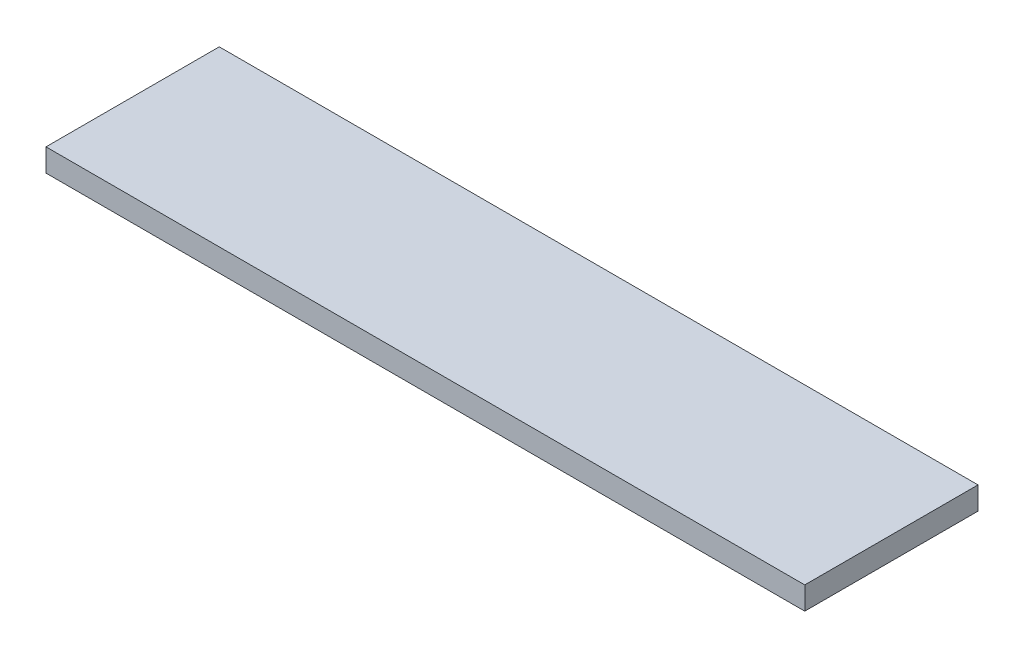
SolidWorks part; units mm, degrees
ref_plane "Спереди" through (0, 0, 0) normal (0, 0, 1) x (1, 0, 0)
ref_plane "Сверху" through (0, 0, 0) normal (0, 1, 0) x (1, 0, 0)
ref_plane "Справа" through (0, 0, 0) normal (1, 0, 0) x (0, 0, -1)
sketch "Эскиз1" plane through (0, 0, 0) normal (0, 1, 0) x (1, 0, 0)
  line L1 (300, -68.5) -> (-300, -68.5)
  line L2 (300, -68.5) -> (300, 68.5)
  line L3 (300, 68.5) -> (-300, 68.5)
  line L4 (-300, -68.5) -> (-300, 68.5)
  line L5 (300, -68.5) -> (-300, 68.5) construction
  line L6 (300, 68.5) -> (-300, -68.5) construction
  point P0 (0, 0)
  dimension "D1" = 600
  dimension "D2" = 137
extrude "Бобышка-Вытянуть1" add sketch "Эскиз1" along normal blind 18
